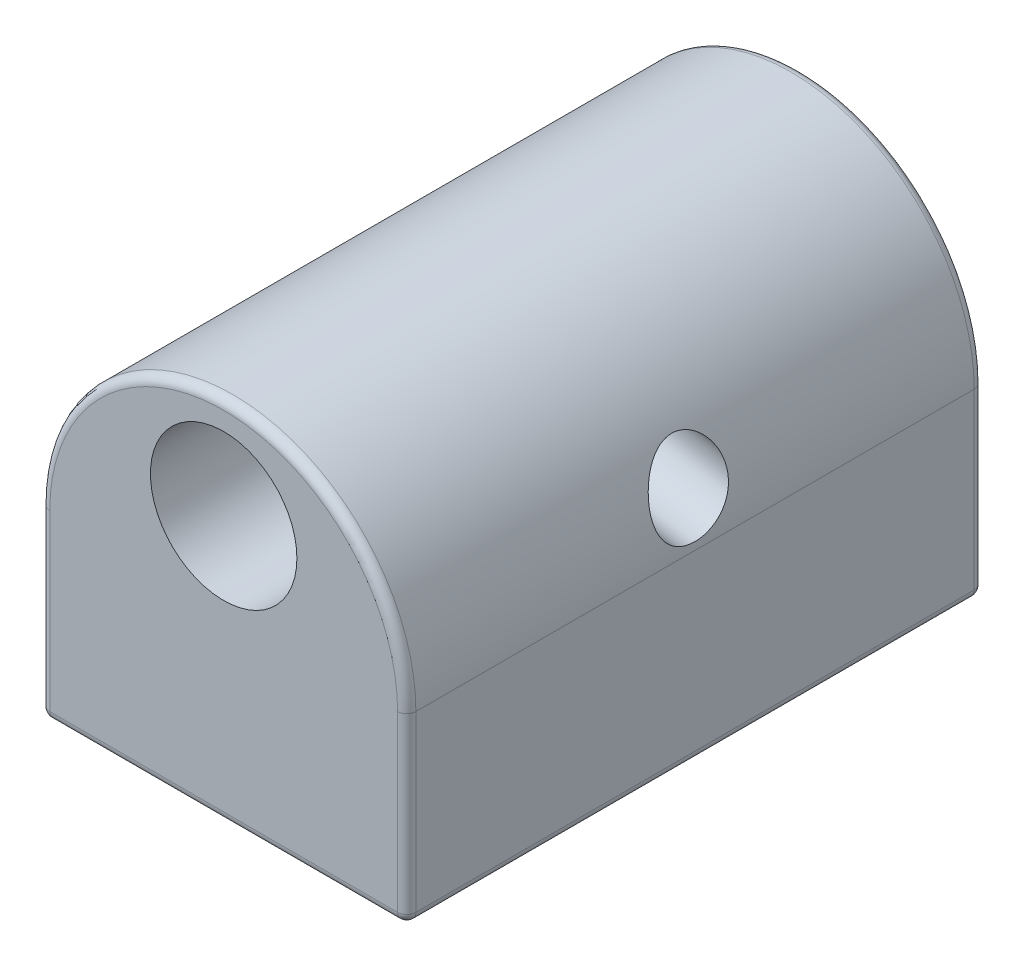
SolidWorks part; units mm, degrees
material "XC38"
ref_plane "Face" through (0, 0, 0) normal (0, 0, 1) x (1, 0, 0)
ref_plane "Dessus" through (0, 0, 0) normal (0, 1, 0) x (1, 0, 0)
ref_plane "Droite" through (0, 0, 0) normal (1, 0, 0) x (0, 0, -1)
sketch "Esquisse1" plane through (0, 0, 0) normal (0, 0, 1) x (1, 0, 0)
  line L0 (-10, 0) -> (-10, -10)
  line L1 (10, 0) -> (10, -10)
  line L2 (10, -10) -> (-10, -10)
  line L3 (0, 10) -> (0, 8.5) construction
  arc A0 (10, 0) -> (-10, 0) centre (0, 0) ccw
  circle A1 centre (0, 4.5) radius 4
  point P1 (0, 10)
  dimension "D3" = 8
  dimension "D1" = 20
  dimension "D2" = 20
  dimension "D4" = 1.5
extrude "Boss.-Extru.1" add sketch "Esquisse1" along normal mid plane 31.5
hole_wizard "Trou taraudé M101" positions "Esquisse3" profile "Esquisse2" tap size "M10" standard "ISO"
sketch "Esquisse3" plane through (0, -10, 0) normal (0, -1, 0) x (-1, 0, 0)
  point P0 (0, 0)
sketch "Esquisse2" plane through (0, -10, 0) normal (1, 0, 0) x (0, 0, -1)
  line L0 (0, 0) -> (0, 17.5537)
  line L1 (0, 17.5537) -> (4.25, 15)
  line L2 (4.25, 15) -> (4.25, 0)
  line L5 (4.25, 0) -> (0, 0)
  line L10 (0, 17.5537) -> (-4.25, 15) construction
  line L11 (0, -6.35) -> (0, 107.95) construction
  dimension "Diamètre du trou pour taraudage" = 8.5
  dimension "Profondeur du trou pour taraudage" = 15
  dimension "Angle de pointe" = 118
cosmetic thread "Filetage de perçage1" parameters "D1"=11, "D2"=10
ref_plane "Plan1" through (9.6985, -1.7101, 0) normal (-0.9848, 0.1736, 0) x (0, 0, -1)
hole_wizard "Trou taraudé M51" positions "Esquisse5" profile "Esquisse4" tap size "M5" standard "ISO"
sketch "Esquisse5" plane through (9.6985, -1.7101, 0) normal (-0.9848, 0.1736, 0) x (0, 0, -1)
  line L0 (-15.75, -1.7365) -> (15.75, -1.7365) construction
  point P0 (0, -4.2365)
  dimension "D1" = 2.5
sketch "Esquisse4" plane through (10.4341, 2.462, 0) normal (0, 0, 1) x (0.1736, 0.9848, 0)
  line L0 (0, 0) -> (0, 11.2618)
  line L1 (0, 11.2618) -> (2.1, 10)
  line L2 (2.1, 10) -> (2.1, 0)
  line L5 (2.1, 0) -> (0, 0)
  line L10 (0, 11.2618) -> (-2.1, 10) construction
  line L11 (0, -6.35) -> (0, 107.95) construction
  dimension "Diamètre du trou pour taraudage" = 4.2
  dimension "Profondeur du trou pour taraudage" = 10
  dimension "Angle de pointe" = 118
cosmetic thread "Filetage de perçage2" parameters "D1"=7.1371, "D2"=5
fillet "Congé1" radius 0.5 10 edges at (10, -5, 15.75) (-10, -5, 15.75) (-10, -5, -15.75) (0, 10, -15.75) (0, 10, 15.75) (10, -5, -15.75) (-10, -10, 0) (0, -10, 15.75) (10, -10, 0) (0, -10, -15.75)
